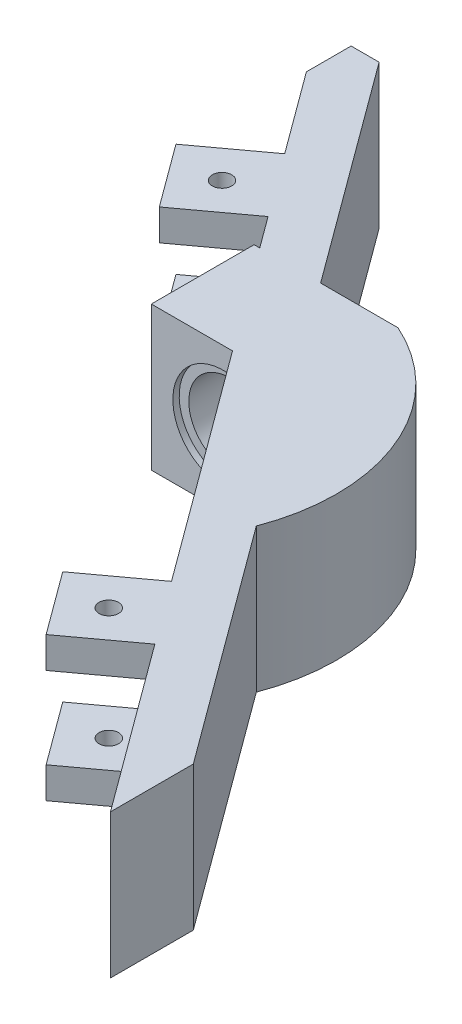
SolidWorks part; units mm, degrees
ref_plane "Front Plane" through (0, 0, 0) normal (0, 0, 1) x (1, 0, 0)
ref_plane "Top Plane" through (0, 0, 0) normal (0, 1, 0) x (1, 0, 0)
ref_plane "Right Plane" through (0, 0, 0) normal (1, 0, 0) x (0, 0, -1)
sketch "Sketch1" plane through (0, 0, 0) normal (0, 1, 0) x (1, 0, 0)
  line L0 (0, 0) -> (0, 5.75)
  line L1 (0, 5.75) -> (3.6, 5.75)
  line L2 (3.6, 5.75) -> (77.6181, -94.979)
  line L3 (0, 0) -> (69.7928, -94.979)
  line L4 (69.7928, -94.979) -> (77.6181, -94.979)
  dimension "D1" = 125
  dimension "D2" = 3.6
  dimension "D3" = 5.75
  dimension "D4" = 6.3058
extrude "Boss-Extrude1" add sketch "Sketch1" along normal blind 18.5
ref_plane "Plane1" through (0, 0, 30) normal (0, 0, 1) x (1, 0, 0)
ref_plane "Plane2" through (0, 9.25, 0) normal (0, 1, 0) x (1, 0, 0)
sketch "Sketch2" plane through (0, 9.25, 0) normal (0, 1, 0) x (1, 0, 0)
  line L0 (15.8842, -22.6035) -> (15.8842, -35.8159)
  line L2 (25.1342, -8.4764) -> (25.1342, -62.3921) construction
  line L5 (15.8842, -35.8159) -> (34.3842, -35.8159)
  line L6 (34.3842, -35.8159) -> (34.3842, -22.6035)
  line L7 (34.3842, -22.6035) -> (15.8842, -22.6035)
  dimension "D1" = 18.5
extrude "Boss-Extrude2" add sketch "Sketch2" along normal mid plane 18.5
sketch "Sketch4" plane through (0, 0, 30) normal (0, 0, 1) x (1, 0, 0)
  line L0 (42.6899, 9.25) -> (-42.6899, 9.25) construction
  line L1 (15.8842, 18.5) -> (15.8842, 0) construction
  circle A0 centre (25.1342, 9.25) radius 5.25
  dimension "D1" = 10.5
  dimension "D2" = 9.25
extrude "Cut-Extrude1" cut sketch "Sketch4" against normal through all both and the other way through all
sketch "Sketch5" plane through (0, 0, 30) normal (0, 0, 1) x (1, 0, 0)
  line L0 (42.6899, 9.25) -> (-42.6899, 9.25) construction
  circle A0 centre (25.1505, 9.25) radius 6.5
  dimension "D1" = 13
sketch "Sketch6" plane through (0, 9.25, 0) normal (0, 1, 0) x (1, 0, 0)
  line L0 (34.3842, -22.6035) -> (34.1437, -35.8159)
  line L1 (77.6181, -94.979) -> (34.1437, -35.8159) construction
  line L2 (34.1437, -35.8159) -> (47.3473, -53.7844)
  arc A0 (34.3842, -22.6035) -> (47.3473, -53.7844) centre (24.3641, -45.0544) cw
extrude "Boss-Extrude3" add sketch "Sketch6" along normal mid plane 18.5
extrude "Cut-Extrude3" cut sketch "Sketch5" along normal blind 11.5 from offset 5
sketch "Sketch7" plane through (0, 0, 0) normal (-0.8058, 0, 0.5921) x (0.5921, 0, 0.8058)
  line L0 (13.0499, 0) -> (13.0499, 4)
  line L1 (0, 0) -> (28.0499, 0) construction
  line L2 (13.0499, 4) -> (23.0499, 4)
  line L3 (23.0499, 4) -> (23.0499, 0)
  line L4 (23.0499, 0) -> (13.0499, 0)
  line L5 (13.0499, 18.5) -> (13.0499, 14.5)
  line L6 (0, 18.5) -> (28.0499, 18.5) construction
  line L7 (13.0499, 14.5) -> (23.0499, 14.5)
  line L8 (23.0499, 14.5) -> (23.0499, 18.5)
  line L9 (13.0499, 18.5) -> (23.0499, 18.5)
  dimension "D1" = 4
  dimension "D2" = 4
  dimension "D3" = 10
  dimension "D4" = 10
  dimension "D5" = 5
  dimension "D6" = 5
  dimension "D7" = 10
extrude "Boss-Extrude4" add sketch "Sketch7" along normal blind 10
sketch "Sketch8" plane through (0, 0, 0) normal (-0.8058, 0, 0.5921) x (0.5921, 0, 0.8058)
  line L0 (44.4459, 0) -> (117.8645, 0) construction
  line L1 (81.1552, 0) -> (91.1552, 0)
  line L2 (81.1552, 0) -> (81.1552, 4)
  line L3 (81.1552, 4) -> (91.1552, 4)
  line L4 (91.1552, 0) -> (91.1552, 4)
  line L5 (44.4459, 18.5) -> (117.8645, 18.5) construction
  line L6 (81.1552, 18.5) -> (91.1552, 18.5)
  line L7 (81.1552, 18.5) -> (81.1552, 14.5)
  line L8 (81.1552, 14.5) -> (91.1552, 14.5)
  line L9 (91.1552, 18.5) -> (91.1552, 14.5)
  dimension "D1" = 4
  dimension "D2" = 4
  dimension "D3" = 10
  dimension "D4" = 10
extrude "Boss-Extrude5" add sketch "Sketch8" along normal blind 10
sketch "Sketch9" plane through (0, 18.5, 0) normal (0, 1, 0) x (1, 0, 0)
  line L0 (-0.3309, -16.4375) -> (7.7274, -10.516) construction
  line L1 (5.5906, -24.4958) -> (-0.3309, -16.4375) construction
  line L2 (45.9188, -79.3772) -> (39.9973, -71.3189) construction
  line L3 (45.9188, -79.3772) -> (53.9771, -73.4558) construction
  circle A0 centre (6.659, -17.5059) radius 1.25
  circle A1 centre (46.9872, -72.3873) radius 1.25
  point P10 (42.958, -75.348)
  dimension "D1" = 5
  dimension "D2" = 5
  dimension "D3" = 2.5
  dimension "D5" = 5
  dimension "D6" = 2.5
  dimension "D4" = 5
extrude "Cut-Extrude4" cut sketch "Sketch9" against normal through all both and the other way through all
sketch "Sketch10" plane through (0, 18.5, 0) normal (0, 1, 0) x (1, 0, 0)
  line L1 (69.7928, -84.3298) -> (69.7928, -94.979)
  line L2 (69.7928, -94.979) -> (77.6181, -94.979)
  line L3 (77.6181, -94.979) -> (69.7928, -84.3298)
  line L4 (77.6181, -94.979) -> (47.3473, -53.7844) construction
extrude "Cut-Extrude5" cut sketch "Sketch10" against normal up to next
